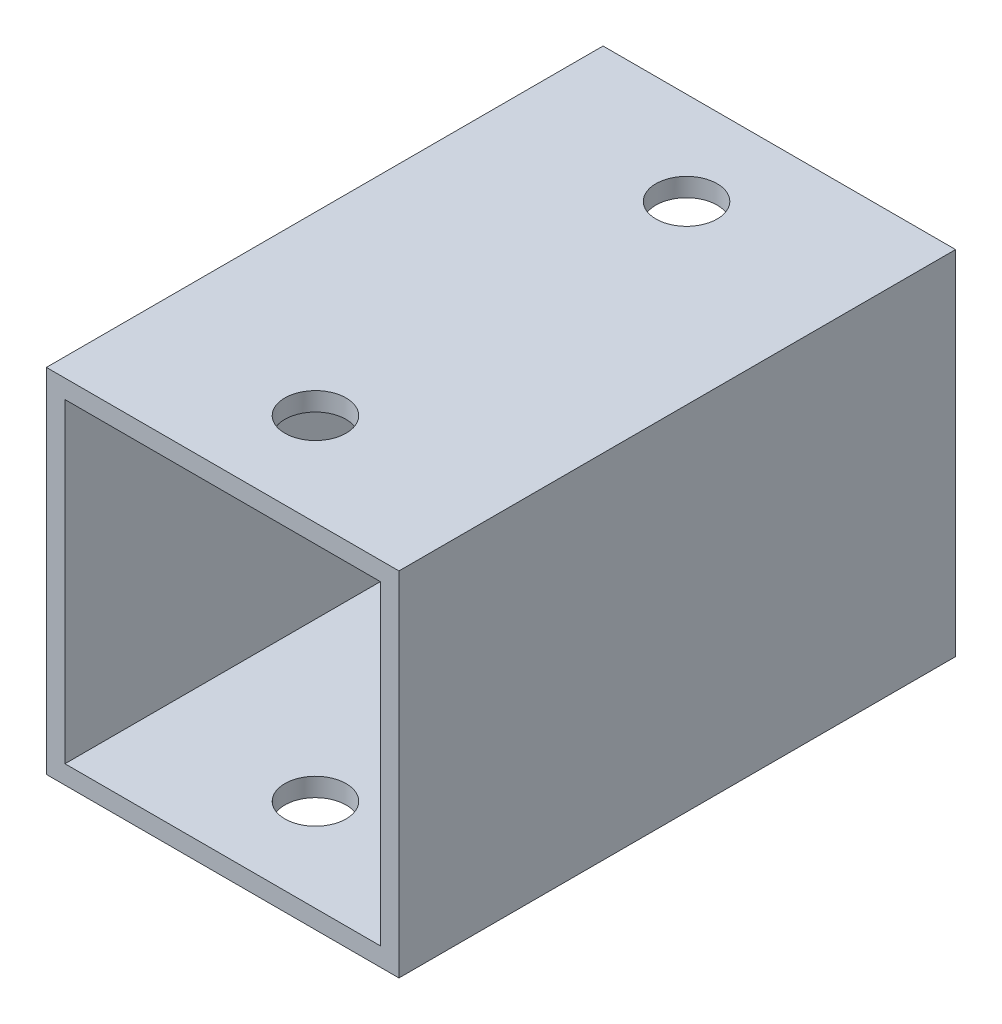
SolidWorks part; units mm, degrees
material "Gerais  - 6061-T6"
ref_plane "Plano frontal" through (0, 0, 0) normal (0, 0, 1) x (1, 0, 0)
ref_plane "Plano superior" through (0, 0, 0) normal (0, 1, 0) x (1, 0, 0)
ref_plane "Plano direito" through (0, 0, 0) normal (1, 0, 0) x (0, 0, -1)
sketch "Esboço1" plane through (0, 0, 0) normal (0, 0, 1) x (1, 0, 0)
  line L1 (0, 0) -> (19, 0)
  line L2 (0, 0) -> (0, 19)
  line L3 (0, 19) -> (19, 19)
  line L4 (19, 0) -> (19, 19)
  dimension "D1" = 19
extrude "Ressalto-extrusão1" add sketch "Esboço1" along normal blind 30
shell "Casca1" thickness 1
sketch "Esboço2" plane through (0, 19, 0) normal (0, 1, 0) x (1, 0, 0)
  line L0 (19, 0) -> (0, 0) construction
  line L1 (19, -30) -> (0, -30) construction
  circle A1 centre (9.5, -25) radius 1.65
  circle A6 centre (9.5, -5) radius 1.65
  point P2 (9.5, 0)
  dimension "D1" = 3.3
  dimension "D2" = 5
  dimension "D3" = 5
extrude "Corte-extrusão1" cut sketch "Esboço2" against normal through all
